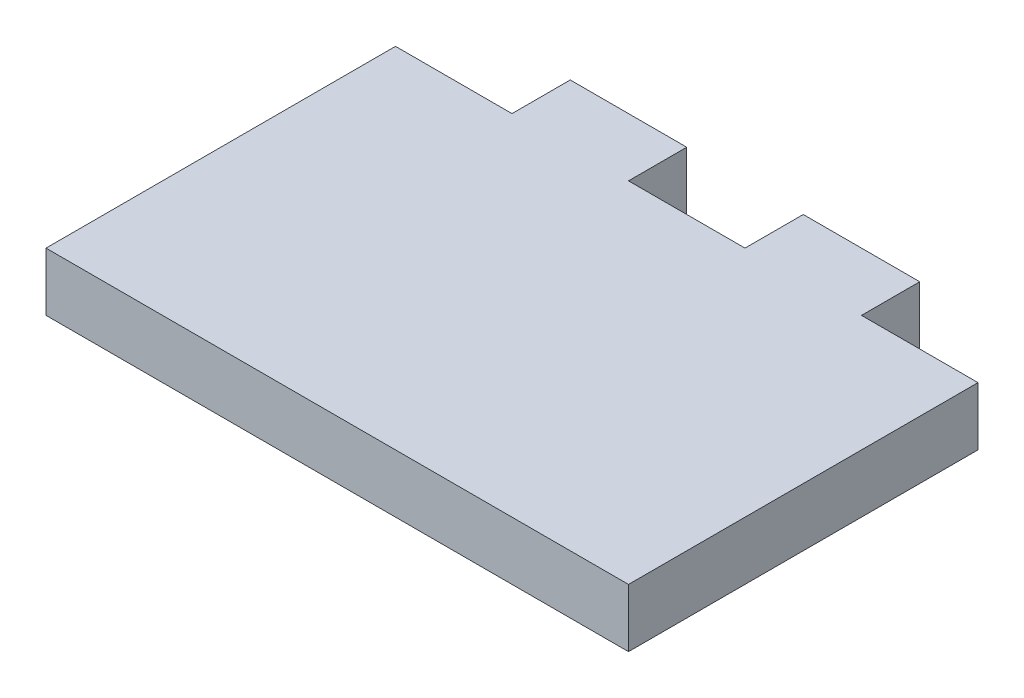
SolidWorks part; units mm, degrees
ref_plane "Front Plane" through (0, 0, 0) normal (0, 0, 1) x (1, 0, 0)
ref_plane "Top Plane" through (0, 0, 0) normal (0, 1, 0) x (1, 0, 0)
ref_plane "Right Plane" through (0, 0, 0) normal (1, 0, 0) x (0, 0, -1)
sketch "Sketch1" plane through (0, 0, 0) normal (0, 1, 0) x (1, 0, 0)
  line L0 (-30, 35) -> (-40, 35)
  line L1 (0, 0) -> (-50, 0)
  line L2 (0, 0) -> (0, 30)
  line L3 (-10, 35) -> (-20, 35)
  line L4 (-50, 0) -> (-50, 30)
  line L8 (-50, 30) -> (-40, 30)
  line L10 (-40, 30) -> (-40, 35)
  line L11 (-30, 35) -> (-30, 30)
  line L12 (-30, 30) -> (-20, 30)
  line L13 (-20, 30) -> (-20, 35)
  line L14 (-10, 35) -> (-10, 30)
  line L15 (-10, 30) -> (0, 30)
  dimension "D1" = 5
  dimension "D2" = 30
  dimension "D3" = 5
  dimension "D4" = 30
extrude "Boss-Extrude2" add sketch "Sketch1" along normal blind 5
